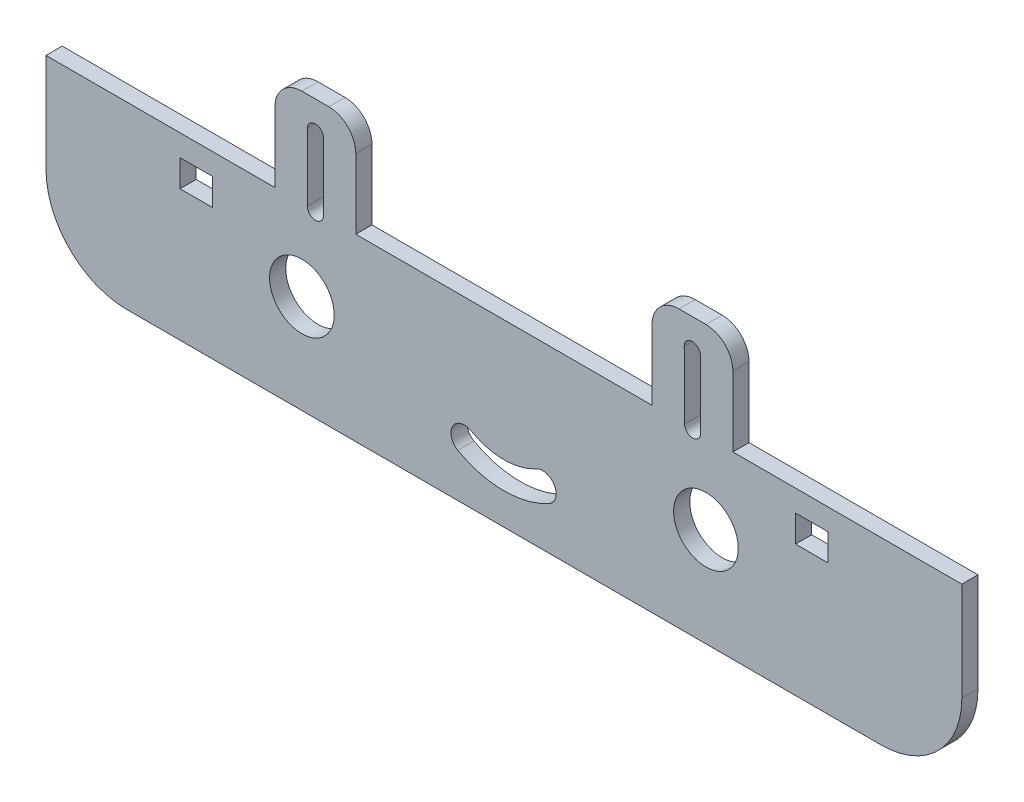
SolidWorks part; units mm, degrees
ref_plane "Front" through (0, 0, 0) normal (0, 0, 1) x (1, 0, 0)
ref_plane "Top" through (0, 0, 0) normal (0, 1, 0) x (1, 0, 0)
ref_plane "Right" through (0, 0, 0) normal (1, 0, 0) x (0, 0, -1)
sketch "Sketch1" plane through (0, 0, 0) normal (0, 0, 1) x (1, 0, 0)
  line L0 (-103.5536, -48) -> (-61.0536, -48)
  line L1 (23.9464, -48) -> (66.4464, -48)
  line L2 (-61.0536, -30) -> (-46.0536, -30)
  line L3 (-53.5536, -48) -> (-53.5536, -35.5) construction
  line L4 (-46.0536, -30) -> (-46.0536, -48)
  line L5 (-46.0536, -48) -> (8.9464, -48)
  line L6 (8.9464, -48) -> (8.9464, -30)
  line L7 (8.9464, -30) -> (23.9464, -30)
  line L8 (-55.0536, -48) -> (-55.0536, -35.5)
  line L9 (-52.0536, -48) -> (-52.0536, -35.5)
  line L10 (16.4742, -47.9999) -> (16.4187, -35.5001) construction
  line L11 (14.9742, -48.0066) -> (14.9187, -35.5067)
  line L12 (23.9464, -30) -> (23.9464, -48)
  line L13 (-61.0536, -30) -> (-61.0536, -48)
  line L14 (17.9741, -47.9933) -> (17.9187, -35.4934)
  line L15 (51.4464, -81.3485) -> (-88.5536, -81.3485)
  line L16 (-103.5536, -66.3485) -> (-103.5536, -48)
  line L17 (66.4464, -48) -> (66.4464, -66.3485)
  arc A0 (-88.5536, -81.3485) -> (-103.5536, -66.3485) centre (-88.5536, -66.3485) cw
  arc A1 (51.4464, -81.3485) -> (66.4464, -66.3485) centre (51.4464, -66.3485) ccw
  arc A4 (-55.0536, -48) -> (-52.0536, -48) centre (-53.5536, -48) ccw
  arc A5 (-52.0536, -35.5) -> (-55.0536, -35.5) centre (-53.5536, -35.5) ccw
  arc A6 (14.9742, -48.0066) -> (17.9741, -47.9933) centre (16.4742, -47.9999) ccw
  arc A7 (17.9187, -35.4934) -> (14.9187, -35.5067) centre (16.4187, -35.5001) ccw
  point P16 (-18.5536, -81.3485)
  point P19 (-53.5536, -41.75)
  point P26 (16.4464, -41.75)
  point P31 (66.4464, -81.3485)
  dimension "D7" = 170
  dimension "D8" = 7.5
  dimension "D10" = 33.3485
  dimension "D11" = 15
  dimension "D12" = 18
  dimension "D13" = 18
  dimension "D17" = 42.5
  dimension "D19" = 1.5
  dimension "D2" = 42.5
  dimension "D3" = 15
  dimension "D4" = 15
  dimension "D5" = 12.5
  dimension "D6" = 12.5
  dimension "D9" = 7.5
extrude "Boss-Extrude1" add sketch "Sketch1" along normal blind 3
fillet "Fillet2" radius 5 4 edges at (8.9464, -30, 1.5) (23.9464, -30, 1.5) (-46.0536, -30, 1.5) (-61.0536, -30, 1.5)
sketch "Sketch3" plane through (0, 0, 3) normal (0, 0, 1) x (1, 0, 0)
  line L3 (-61.0536, -48) -> (-103.5536, -48) construction
  line L5 (-18.5536, -48) -> (-18.5536, -58) construction
  line L6 (8.9464, -48) -> (-46.0536, -48) construction
  circle A0 centre (-56.0536, -63) radius 6
  circle A1 centre (18.9464, -63) radius 6
  arc A2 (-25.8846, -71.0865) -> (-11.357, -71.1609) centre (-18.5536, -58) ccw construction
  arc A3 (-27.1064, -73.2676) -> (-10.1576, -73.3544) centre (-18.5536, -58) ccw
  arc A4 (-24.6627, -68.9054) -> (-12.5564, -68.9674) centre (-18.5536, -58) ccw
  arc A5 (-24.6627, -68.9054) -> (-27.1064, -73.2676) centre (-25.8846, -71.0865) ccw
  arc A6 (-10.1576, -73.3544) -> (-12.5564, -68.9674) centre (-11.357, -71.1609) ccw
  point P15 (-18.6304, -72.9998)
  dimension "D3" = 12
  dimension "D6" = 2.5
  dimension "D1" = 15
  dimension "D5" = 15
  dimension "D2" = 10
  dimension "D4" = 10
extrude "Cut-Extrude1" cut sketch "Sketch3" against normal blind 10
sketch "Sketch4" plane through (0, 0, 3) normal (0, 0, 1) x (1, 0, 0)
  line L0 (35.5678, -52) -> (35.5678, -57)
  line L1 (-78.675, -52) -> (-72.675, -52)
  line L2 (-78.675, -52) -> (-78.675, -57)
  line L3 (-78.675, -57) -> (-72.675, -57)
  line L4 (-72.675, -57) -> (-72.675, -52)
  line L5 (-61.0536, -48) -> (-103.5536, -48) construction
  line L6 (-18.5536, -48) -> (-18.5536, -42.3392) construction
  line L7 (8.9464, -48) -> (-46.0536, -48) construction
  line L8 (35.5678, -57) -> (41.5678, -57)
  line L9 (41.5678, -57) -> (41.5678, -52)
  line L10 (66.4464, -48) -> (23.9464, -48) construction
  line L11 (41.5678, -52) -> (35.5678, -52)
  dimension "D1" = 5
  dimension "D2" = 6
  dimension "D3" = 4
  dimension "D4" = 4
  dimension "D5" = 5
extrude "Cut-Extrude2" cut sketch "Sketch4" against normal blind 10
